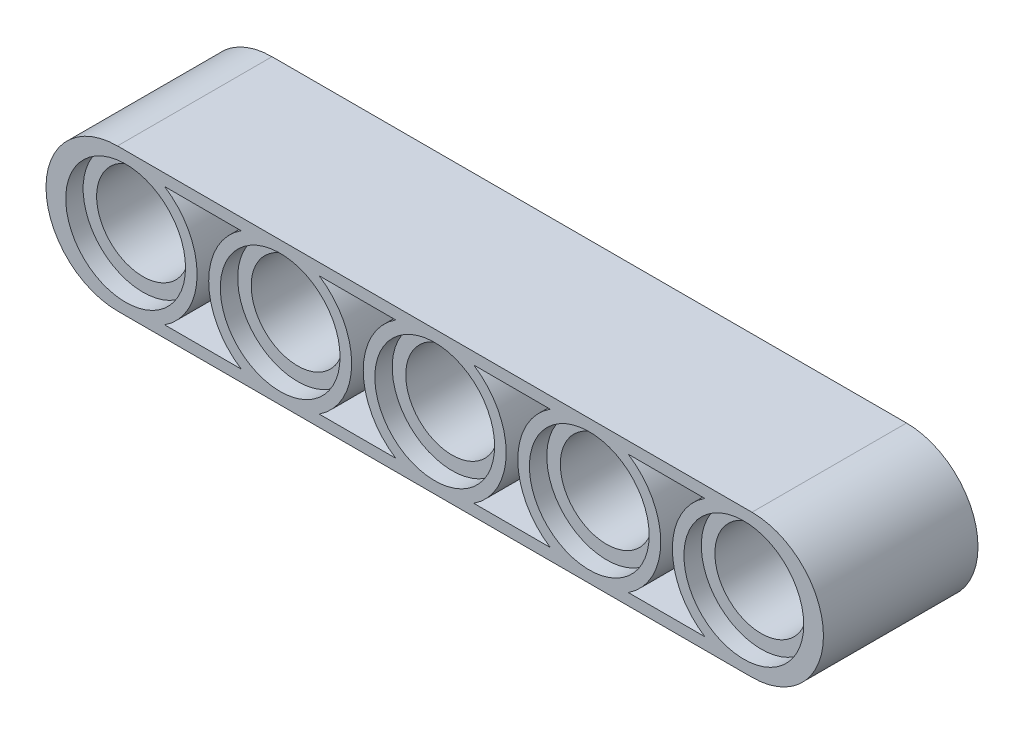
SolidWorks part; units mm, degrees
ref_plane "Front Plane" through (0, 0, 0) normal (0, 0, 1) x (1, 0, 0)
ref_plane "Top Plane" through (0, 0, 0) normal (0, 1, 0) x (1, 0, 0)
ref_plane "Right Plane" through (0, 0, 0) normal (1, 0, 0) x (0, 0, -1)
sketch "Sketch1" plane through (0, 0, 0) normal (0, 0, 1) x (1, 0, 0)
  line L0 (-16, 0) -> (16, 0) construction
  line L3 (-16, 3.1) -> (16, 3.1)
  line L4 (-16, -3.1) -> (16, -3.1)
  line L5 (-16.4214, 0) -> (16.4214, 0) construction
  line L6 (-16.4214, 3.7) -> (16.4214, 3.7)
  line L7 (-16.4214, -3.7) -> (16.4214, -3.7)
  arc A2 (-16, 3.1) -> (-16, -3.1) centre (-16, 0) ccw
  arc A3 (16, -3.1) -> (16, 3.1) centre (16, 0) ccw
  arc A4 (-16.4214, 3.7) -> (-16.4214, -3.7) centre (-16.4214, 0) ccw
  arc A5 (16.4214, -3.7) -> (16.4214, 3.7) centre (16.4214, 0) ccw
  point P2 (0, 0)
  point P7 (0, 0)
extrude "Outer Shape" add sketch "Sketch1" along normal blind 4
sketch "Sketch2" plane through (0, 0, 0) normal (0, 0, 1) x (1, 0, 0)
  line L0 (-15.9189, 0) -> (15.9189, 0) construction
  line L3 (-15.9189, 3.1896) -> (15.9189, 3.1896)
  line L4 (-15.9189, -3.1896) -> (15.9189, -3.1896)
  line L5 (-16.4214, 0) -> (16.4214, 0) construction
  line L6 (-16.4214, 3.7) -> (16.4214, 3.7)
  line L7 (-16.4214, -3.7) -> (16.4214, -3.7)
  arc A2 (-15.9189, 3.1896) -> (-15.9189, -3.1896) centre (-15.9189, 0) ccw
  arc A3 (15.9189, -3.1896) -> (15.9189, 3.1896) centre (15.9189, 0) ccw
  arc A4 (-16.4214, 3.7) -> (-16.4214, -3.7) centre (-16.4214, 0) ccw
  arc A5 (16.4214, -3.7) -> (16.4214, 3.7) centre (16.4214, 0) ccw
  point P2 (0, 0)
  point P7 (0, 0)
extrude "Middle wall" add sketch "Sketch2" along normal blind 0.1 separate body contours L3 A3 L4 A2
sketch "Holes" plane through (0, 0, 0.1) normal (0, 0, 1) x (1, 0, 0)
  circle A0 centre (-16, 0) radius 3.1
  circle A2 centre (-16, 0) radius 3.7
  circle A3 centre (-16, 0) radius 2.4
  circle A4 centre (-8, 0) radius 3.1
  circle A5 centre (-8, 0) radius 3.7
  circle A6 centre (-8, 0) radius 2.4
  circle A7 centre (0, 0) radius 3.1
  circle A8 centre (0, 0) radius 3.7
  circle A9 centre (0, 0) radius 2.4
  circle A10 centre (8, 0) radius 3.1
  circle A11 centre (8, 0) radius 3.7
  circle A12 centre (8, 0) radius 2.4
  circle A13 centre (16, 0) radius 3.1
  circle A14 centre (16, 0) radius 3.7
  circle A15 centre (16, 0) radius 2.4
  arc M2 (-15.9189, 3.1896) -> (-15.9189, -3.1896) centre (-15.9189, 0) ccw
  line M3 (-15.9189, -3.1896) -> (15.9189, -3.1896)
  arc M4 (15.9189, -3.1896) -> (15.9189, 3.1896) centre (15.9189, 0) ccw
  line M5 (15.9189, 3.1896) -> (-15.9189, 3.1896)
sketch "Sketch3" plane through (0, 0, 0) normal (0, 0, 1) x (1, 0, 0)
  circle A0 centre (-16, 0) radius 3.1
  circle A2 centre (-16, 0) radius 3.7
  circle A3 centre (-16, 0) radius 2.4
  circle A4 centre (-8, 0) radius 3.1
  circle A5 centre (-8, 0) radius 3.7
  circle A6 centre (-8, 0) radius 2.4
  circle A7 centre (0, 0) radius 3.1
  circle A8 centre (0, 0) radius 3.7
  circle A9 centre (0, 0) radius 2.4
  circle A10 centre (8, 0) radius 3.1
  circle A11 centre (8, 0) radius 3.7
  circle A12 centre (8, 0) radius 2.4
  circle A13 centre (16, 0) radius 3.1
  circle A14 centre (16, 0) radius 3.7
  circle A15 centre (16, 0) radius 2.4
extrude "Outer Hole" add sketch "Holes" along normal blind 3.9 contours A5 A4 M5 M3 | A2 A0 M3 M5 M2 | A8 A7 M5 M3 | A11 A10 M5 M3 | A14 A13 M5 M3 M4
sketch "Sketch4" plane through (0, 0, 0) normal (0, 0, 1) x (1, 0, 0)
  circle A0 centre (-16, 0) radius 3.1
  circle A2 centre (-16, 0) radius 3.7
  circle A3 centre (-16, 0) radius 2.4
  circle A4 centre (-8, 0) radius 3.1
  circle A5 centre (-8, 0) radius 3.7
  circle A6 centre (-8, 0) radius 2.4
  circle A7 centre (0, 0) radius 3.1
  circle A8 centre (0, 0) radius 3.7
  circle A9 centre (0, 0) radius 2.4
  circle A10 centre (8, 0) radius 3.1
  circle A11 centre (8, 0) radius 3.7
  circle A12 centre (8, 0) radius 2.4
  circle A13 centre (16, 0) radius 3.1
  circle A14 centre (16, 0) radius 3.7
  circle A15 centre (16, 0) radius 2.4
extrude "Inner Hole" add sketch "Sketch3" along normal blind 3.1 contours A0 | A3 | A4 | A6 | A7 | A9 | A10 | A12 | A13 | A15
extrude "Through Hole" cut sketch "Sketch4" along normal through all contours A3 | A6 | A9 | A12 | A15
mirror "Mirror1" about plane through (-16.4214, 0, 0) normal (0, 0, 1) of bodies 112
